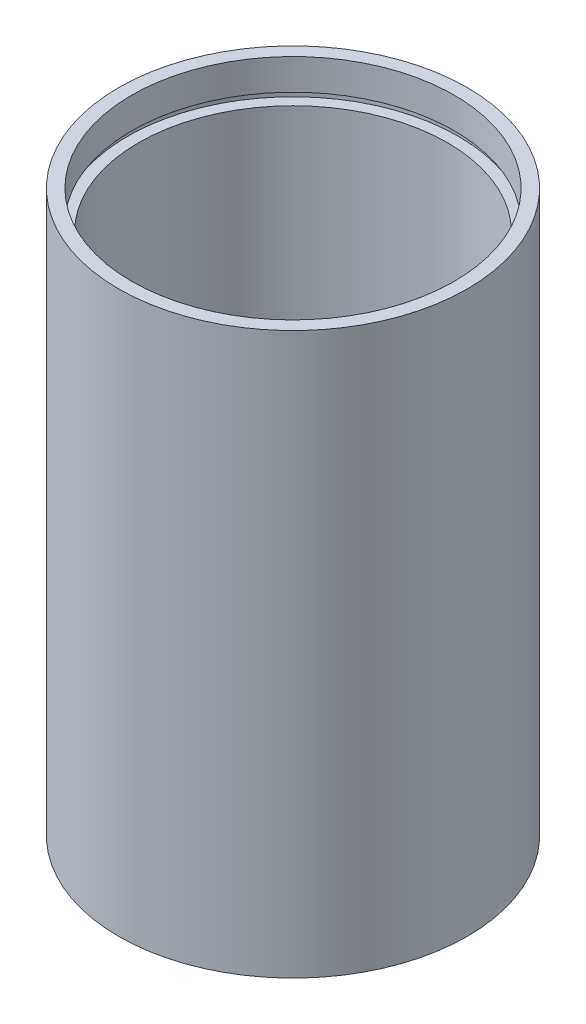
SolidWorks part; units mm, degrees
ref_plane "前视基准面" through (0, 0, 0) normal (0, 0, 1) x (1, 0, 0)
ref_plane "上视基准面" through (0, 0, 0) normal (0, 1, 0) x (1, 0, 0)
ref_plane "右视基准面" through (0, 0, 0) normal (1, 0, 0) x (0, 0, -1)
sketch "草图1" plane through (0, 0, 0) normal (0, 0, 1) x (1, 0, 0)
  line L0 (0, 161.3762) -> (0, 0) construction
  line L1 (141.7365, 0) -> (-131.7984, 0) construction
  line L2 (25.4, 0) -> (25.4, 81.7)
  line L3 (23.5, 0) -> (23.5, 4.5)
  line L4 (24.1, 4.5) -> (24.1, 5.5)
  line L5 (22.5, 5.5) -> (22.5, 76.2)
  line L6 (22.5, 5.5) -> (24.1, 5.5)
  line L7 (24.1, 76.2) -> (24.1, 77.2)
  line L8 (22.5, 76.2) -> (24.1, 76.2)
  line L9 (23.5, 77.2) -> (23.5, 81.7)
  line L10 (24.1, 77.2) -> (23.5, 77.2)
  line L11 (23.5, 81.7) -> (25.4, 81.7)
  line L12 (23.5, 0) -> (25.4, 0)
  line L13 (23.5, 4.5) -> (24.1, 4.5)
  dimension "D1" = 25.4
  dimension "D2" = 23.5
  dimension "D3" = 4.5
  dimension "D4" = 24.1
  dimension "D5" = 22.5
  dimension "D6" = 24.1
  dimension "D7" = 1
  dimension "D8" = 70.7
  dimension "D9" = 76.2
  dimension "D10" = 1
revolve "旋转1" add sketch "草图1" angle 360 about L0
cosmetic thread "装饰螺纹线1" parameters "D2"=48
cosmetic thread "装饰螺纹线2" parameters "D2"=46
cosmetic thread "装饰螺纹线3" parameters "D2"=48
